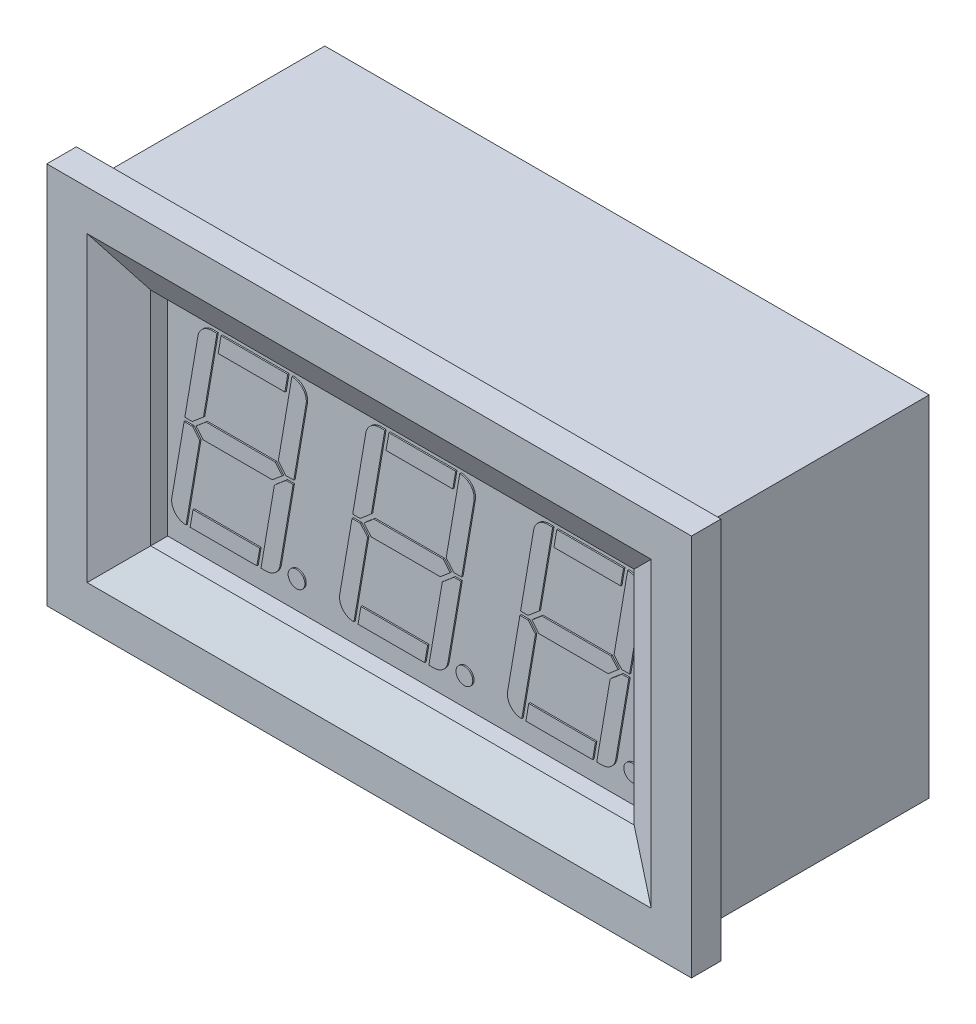
SolidWorks part; units mm, degrees
material "ABS"
ref_plane "Front" through (0, 0, 0) normal (0, 0, 1) x (1, 0, 0)
ref_plane "Up" through (0, 0, 0) normal (0, 1, 0) x (1, 0, 0)
ref_plane "Right" through (0, 0, 0) normal (1, 0, 0) x (0, 0, -1)
sketch "sketch 1" plane through (0, 0, 0) normal (0, 0, 1) x (1, 0, 0)
  line L1 (22.5, -13) -> (-22.5, -13)
  line L2 (22.5, -13) -> (22.5, 13)
  line L3 (22.5, 13) -> (-22.5, 13)
  line L4 (-22.5, -13) -> (-22.5, 13)
  line L5 (22.5, -13) -> (-22.5, 13) construction
  line L6 (22.5, 13) -> (-22.5, -13) construction
  point P0 (0, 0)
  dimension "D1" = 26
  dimension "D2" = 45
extrude "Boss-Extrude1" add sketch "sketch 1" along normal blind 17
sketch "sketch " plane through (0, 0, 17) normal (0, 0, 1) x (1, 0, 0)
  line L1 (24, -14.25) -> (-24, -14.25)
  line L2 (24, -14.25) -> (24, 14.25)
  line L3 (24, 14.25) -> (-24, 14.25)
  line L4 (-24, -14.25) -> (-24, 14.25)
  line L5 (24, -14.25) -> (-24, 14.25) construction
  line L6 (24, 14.25) -> (-24, -14.25) construction
  point P0 (0, 0)
  dimension "D1" = 28.5
  dimension "D2" = 48
extrude "Boss-Extrude2" add sketch "sketch " along normal blind 2.2
sketch "sketch 3" plane through (0, 0, 19.2) normal (0, 0, 1) x (1, 0, 0)
  line L1 (18, -8.25) -> (-18, -8.25)
  line L2 (18, -8.25) -> (18, 8.25)
  line L3 (18, 8.25) -> (-18, 8.25)
  line L4 (-18, -8.25) -> (-18, 8.25)
  line L5 (18, -8.25) -> (-18, 8.25) construction
  line L6 (18, 8.25) -> (-18, -8.25) construction
  point P0 (0, 0)
  dimension "D1" = 36
  dimension "D2" = 16.5
extrude "Cut-Extrude1" cut sketch "sketch 3" against normal blind 3
chamfer "chamfer 1" distance 3 angle 30 4 edges at (18, 0, 19.2) (0, 8.25, 19.2) (-18, 0, 19.2) (0, -8.25, 19.2)
sketch "sketch 4" plane through (0, 0, 16.2) normal (0, 0, 1) x (1, 0, 0)
  line L0 (-17.8, -6.75) -> (-16.532, -6.75)
  line L1 (-17.8, -6.75) -> (-16.6756, -0.15)
  line L2 (-9.6847, -6.75) -> (-8.5603, -0.15)
  line L3 (-15.5, 6.75) -> (-14.232, 6.75)
  line L4 (-18, -8.25) -> (18, -8.25) construction
  line L5 (18, 8.25) -> (-18, 8.25) construction
  line L6 (-18, 8.25) -> (-18, -8.25) construction
  line L7 (-8.5347, 0) -> (-16.65, 0) construction
  line L8 (-8.5092, 0.15) -> (-9.099, 0.15)
  line L9 (-9.099, 0.15) -> (-9.6633, 0.8185)
  line L10 (-9.6633, 0.8185) -> (-8.6527, 6.75)
  line L11 (-8.5603, -0.15) -> (-9.0776, -0.15)
  line L12 (-9.0776, -0.15) -> (-9.9544, -0.89)
  line L13 (-9.9544, -0.89) -> (-10.9527, -6.75)
  line L14 (-16.6244, 0.15) -> (-16.0714, 0.15)
  line L15 (-16.0714, 0.15) -> (-15.2364, 0.8548)
  line L16 (-15.2364, 0.8548) -> (-14.232, 6.75)
  line L17 (-16.6756, -0.15) -> (-16.05, -0.15)
  line L18 (-16.05, -0.15) -> (-15.5154, -0.7833)
  line L19 (-15.5154, -0.7833) -> (-16.532, -6.75)
  line L20 (-15.784, 0) -> (-15.0435, 0.625)
  line L21 (-15.0435, 0.625) -> (-9.8925, 0.625)
  line L22 (-9.8925, 0.625) -> (-9.365, 0)
  line L23 (-9.365, 0) -> (-10.1055, -0.625)
  line L24 (-10.1055, -0.625) -> (-15.2565, -0.625)
  line L25 (-15.2565, -0.625) -> (-15.784, 0)
  line L26 (-9.8925, 0.625) -> (-10.1055, -0.625) construction
  line L27 (-15.0435, 0.625) -> (-15.2565, -0.625) construction
  line L28 (-9.6633, 0.8185) -> (-9.8925, 0.625) construction
  line L29 (-15.2364, 0.8548) -> (-15.0435, 0.625) construction
  line L30 (-13.9277, 6.75) -> (-14.1406, 5.5)
  line L31 (-14.1406, 5.5) -> (-9.17, 5.5)
  line L32 (-9.17, 5.5) -> (-8.9571, 6.75)
  line L33 (-16.2277, -6.75) -> (-16.0147, -5.5)
  line L34 (-16.0147, -5.5) -> (-11.0441, -5.5)
  line L35 (-11.0441, -5.5) -> (-11.2571, -6.75)
  line L36 (-10.9527, -6.75) -> (-9.6847, -6.75)
  line L37 (-16.2277, -6.75) -> (-11.2571, -6.75)
  line L38 (-8.5092, 0.15) -> (-7.3847, 6.75)
  line L39 (-8.6527, 6.75) -> (-7.3847, 6.75)
  line L40 (-13.9277, 6.75) -> (-8.9571, 6.75)
  line L41 (-16.6244, 0.15) -> (-15.5, 6.75)
  line L42 (-9.6847, -6.75) -> (-6.2012, -6.75) construction
  circle A0 centre (-8.3102, -6.125) radius 0.625
  dimension "D22" = 1.25
  dimension "D1" = 1.5
  dimension "D2" = 1.5
  dimension "D3" = 0.2
  dimension "D4" = 2.5
  dimension "D5" = 8
  dimension "D6" = 0.15
  dimension "D7" = 1.25
  dimension "D8" = 0.3
  dimension "D9" = 1.25
  dimension "D10" = 1.25
  dimension "D11" = 0.625
  dimension "D12" = 0.3
  dimension "D13" = 0.3
  dimension "D14" = 0.3
  dimension "D15" = 0.3
  dimension "D16" = 40.167
  dimension "D17" = 50
  dimension "D18" = 0.3
  dimension "D19" = 0.3
  dimension "D20" = 1.25
  dimension "D21" = 6.75
  dimension "D23" = 1.25
extrude "Boss-Extrude3" add sketch "sketch 4" along normal blind 0.1
fillet "rounding 1" radius 1.05 4 edges at (-9.6847, -6.75, 16.25) (-17.8, -6.75, 16.25) (-15.5, 6.75, 16.25) (-7.3847, 6.75, 16.25)
pattern_linear "Linear array1" count 3 spacing 12.5 along (1, 0, 0) of "Boss-Extrude3", "rounding 1"
